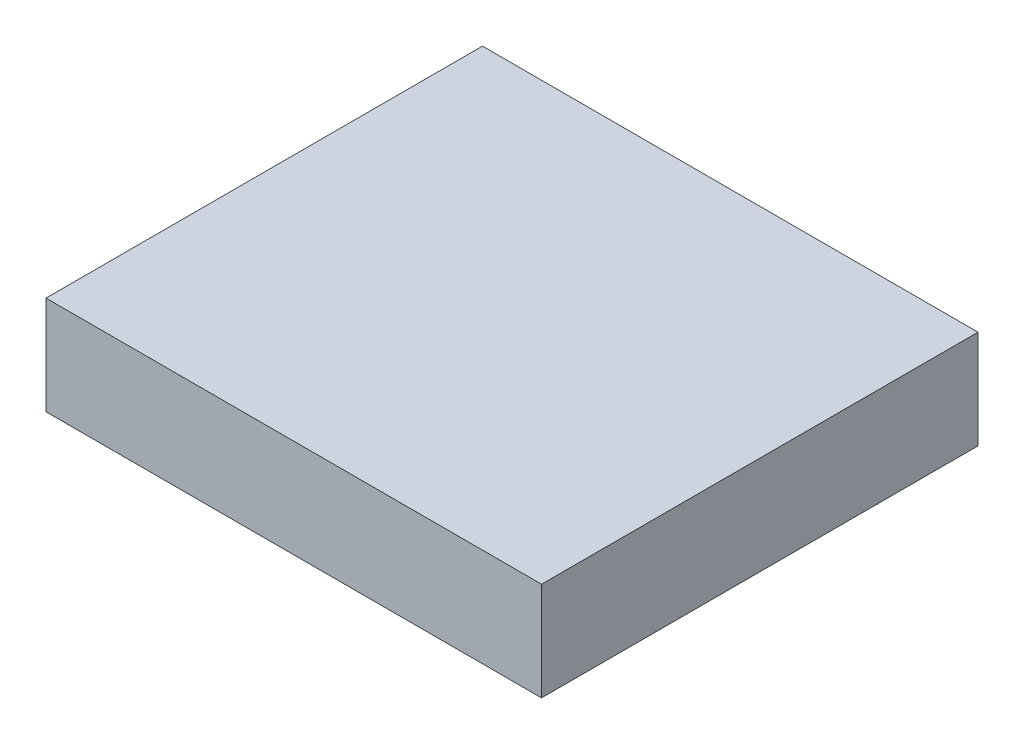
SolidWorks part; units mm, degrees
ref_plane "Front" through (0, 0, 0) normal (0, 0, 1) x (1, 0, 0)
ref_plane "Top" through (0, 0, 0) normal (0, 1, 0) x (1, 0, 0)
ref_plane "Right" through (0, 0, 0) normal (1, 0, 0) x (0, 0, -1)
sketch "Sketch1" plane through (0, 0, 0) normal (0, 1, 0) x (1, 0, 0)
  line L1 (0, 0) -> (15.1, 0)
  line L2 (0, 0) -> (0, -13.3)
  line L3 (0, -13.3) -> (15.1, -13.3)
  line L4 (15.1, 0) -> (15.1, -13.3)
  dimension "D1" = 13.3
  dimension "D2" = 15.1
extrude "Boss-Extrude1" add sketch "Sketch1" along normal blind 3
